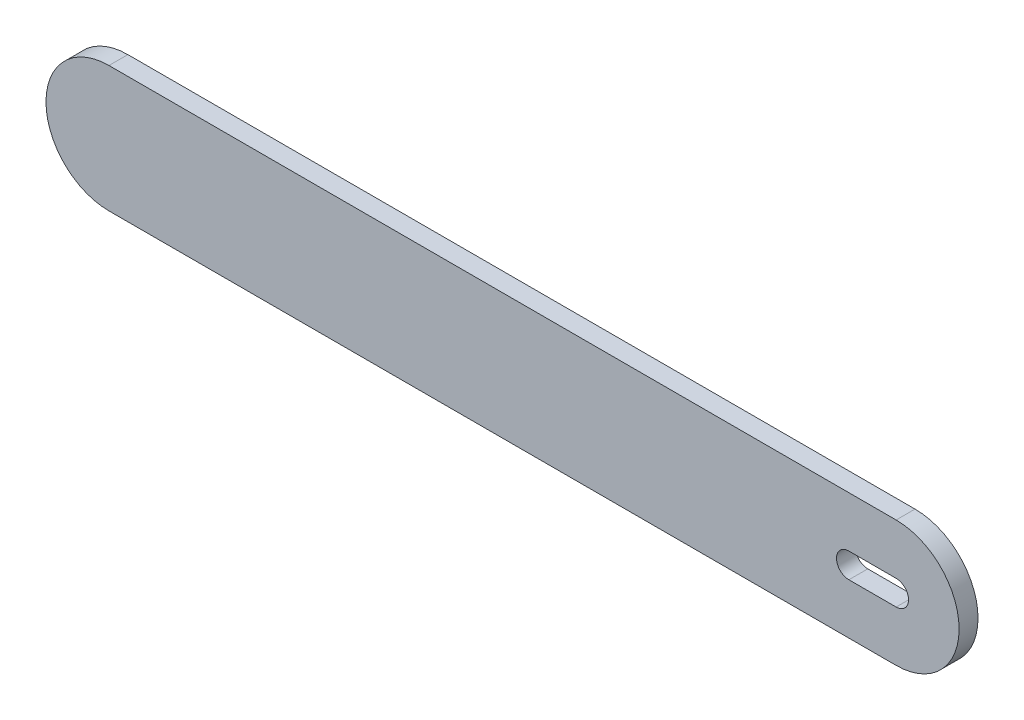
SolidWorks part; units mm, degrees
ref_plane "Front Plane" through (0, 0, 0) normal (0, 0, 1) x (1, 0, 0)
ref_plane "Top Plane" through (0, 0, 0) normal (0, 1, 0) x (1, 0, 0)
ref_plane "Right Plane" through (0, 0, 0) normal (1, 0, 0) x (0, 0, -1)
sketch "Sketch1" plane through (0, 0, 0) normal (0, 0, 1) x (1, 0, 0)
  line L0 (-53.15, -20.3675) -> (-303.15, -20.3675)
  line L1 (-303.15, 19.6325) -> (-53.15, 19.6325)
  arc A0 (-303.15, -20.3675) -> (-303.15, 19.6325) centre (-303.15, -0.3675) cw
  arc A1 (-53.15, 19.6325) -> (-53.15, -20.3675) centre (-53.15, -0.3675) cw
  dimension "D1" = 20
  dimension "D2" = 250
extrude "Boss-Extrude1" add sketch "Sketch1" along normal blind 6
sketch "Sketch2" plane through (0, 0, 0) normal (0, 0, -1) x (-1, 0, 0)
  line L0 (53.15, -0.3675) -> (68.15, -0.3675) construction
  line L2 (53.15, 3.5763) -> (68.15, 3.5763)
  line L3 (53.15, -4.3113) -> (68.15, -4.3113)
  line L4 (53.15, 19.6325) -> (303.15, 19.6325) construction
  arc A0 (53.15, 3.5763) -> (53.15, -4.3113) centre (53.15, -0.3675) ccw
  arc A1 (68.15, -4.3113) -> (68.15, 3.5763) centre (68.15, -0.3675) ccw
  point P5 (60.65, -0.3675)
  dimension "D1" = 15
extrude "Cut-Extrude1" cut sketch "Sketch2" against normal up to next
